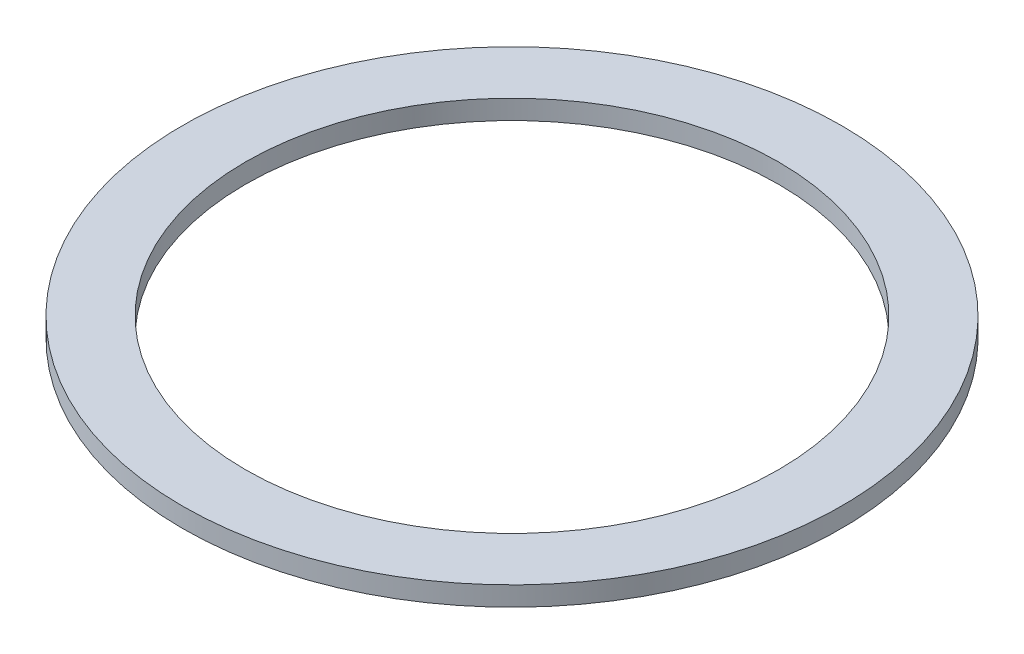
SolidWorks part; units mm, degrees
material "Alloy Steel"
ref_plane "Front Plane" through (0, 0, 0) normal (0, 0, 1) x (1, 0, 0)
ref_plane "Top Plane" through (0, 0, 0) normal (0, 1, 0) x (1, 0, 0)
ref_plane "Right Plane" through (0, 0, 0) normal (1, 0, 0) x (0, 0, -1)
sketch "Sketch1" plane through (0, 0, 0) normal (0, 1, 0) x (1, 0, 0)
  line L0 (-34, 0) -> (34, 0) construction
  line L1 (-27.5, 0) -> (27.5, 0) construction
  point P4 (0, 0)
  point P7 (0, 0)
  dimension "OD" = 68
  dimension "ID" = 55
sketch "Sketch2" plane through (0, 0, 0) normal (0, 0, 1) x (1, 0, 0)
  line L0 (34, -1) -> (34, 1) construction
  point P4 (34, 0)
  dimension "Thickness" = 2
sketch "Sketch3" plane through (0, 0, 0) normal (0, 1, 0) x (1, 0, 0)
  circle A0 centre (0, 0) radius 34
  circle A1 centre (0, 0) radius 27.5
extrude "Boss-Extrude1" add sketch "Sketch3" against normal up to vertex (1 mm away) and the other way up to vertex (1 mm away)
